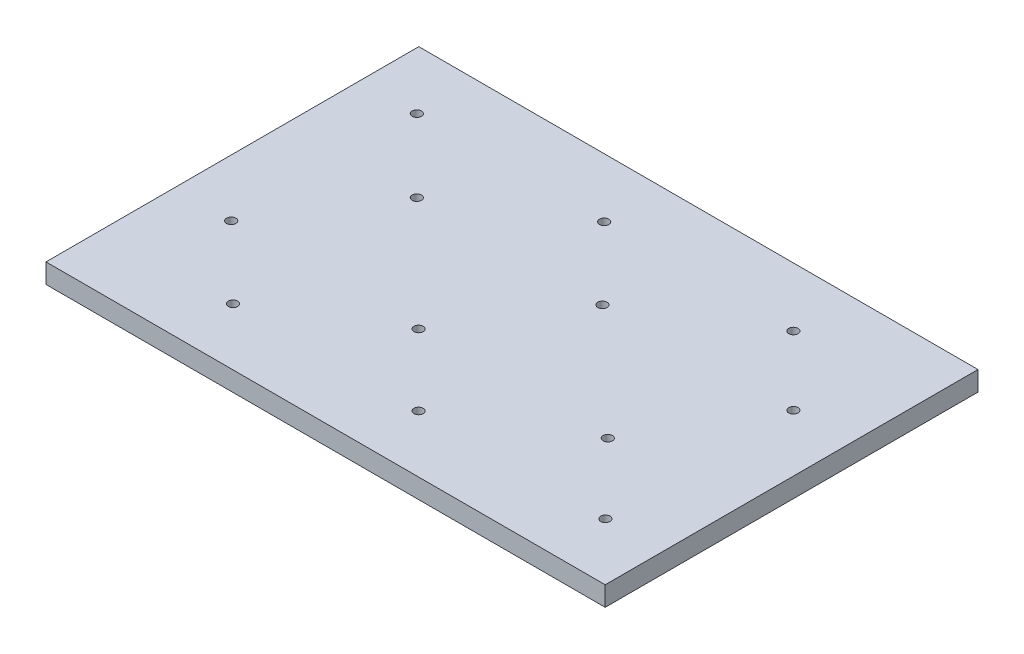
SolidWorks part; units mm, degrees
ref_plane "Front Plane" through (0, 0, 0) normal (0, 0, 1) x (1, 0, 0)
ref_plane "Top Plane" through (0, 0, 0) normal (0, 1, 0) x (1, 0, 0)
ref_plane "Right Plane" through (0, 0, 0) normal (1, 0, 0) x (0, 0, -1)
sketch "Sketch1" plane through (0, 0, 0) normal (0, 1, 0) x (1, 0, 0)
  line L1 (-35, 25) -> (35, 25)
  line L2 (-35, 25) -> (-35, -25)
  line L3 (-35, -25) -> (35, -25)
  line L4 (35, 25) -> (35, -25)
  line L5 (-35, 25) -> (35, -25) construction
  line L6 (-35, -25) -> (35, 25) construction
  point P0 (0, 0)
  dimension "D1" = 70
  dimension "D2" = 50
extrude "Boss-Extrude1" add sketch "Sketch1" along normal blind 6.35
sketch "Sketch2" plane through (0, 6.35, 0) normal (0, 1, 0) x (1, 0, 0)
  line L5 (30, -20) -> (30, 20)
  line L6 (30, -20) -> (30, 20)
  line L11 (30, 20) -> (-30, 20)
  line L12 (-30, 20) -> (-30, -20)
  line L13 (-30, -20) -> (30, -20)
  line L15 (30, 20) -> (-30, 20)
  line L16 (-30, 20) -> (-30, -20)
  line L17 (-30, -20) -> (30, -20)
  dimension "D1" = 5
extrude "Cut-Extrude1" cut sketch "Sketch2" against normal blind 3.175
sketch "Sketch3" plane through (0, 3.175, 0) normal (0, 1, 0) x (1, 0, 0)
  line L1 (-25, 5) -> (-15, 5)
  line L2 (-25, 5) -> (-25, 15)
  line L3 (-25, 15) -> (-15, 15)
  line L4 (-15, 5) -> (-15, 15)
  line L5 (-25, 5) -> (-15, 15) construction
  line L6 (-25, 15) -> (-15, 5) construction
  point P0 (-20, 10)
  dimension "D1" = 10
extrude "Boss-Extrude2" add sketch "Sketch3" along normal blind 0.55
pattern_linear "LPattern1" count 3 spacing 20 along (1, 0, 0) count 2 spacing 20 along (0, 0, 1) of "Boss-Extrude2"
ref_plane "Plane1" through (0, 0, 0) normal (0, 0, 1) x (1, 0, 0)
ref_plane "Plane3" through (0, 0, 0) normal (-1, 0, 0) x (0, 0, 1)
sketch "Sketch10" plane through (0, 3.175, 0) normal (0, 1, 0) x (1, 0, 0)
  line L0 (-10.25, -0.25) -> (-10.25, -20)
  line L1 (-15, 5) -> (-15, 15) construction
  line L2 (-30, 0.25) -> (-10.25, 0.25)
  line L3 (-30, 0.25) -> (-30, -0.25)
  line L4 (-30, -0.25) -> (-10.25, -0.25)
  line L5 (30, 0.25) -> (30, -0.25)
  line L6 (-30, 0.25) -> (30, -0.25) construction
  line L7 (-30, -0.25) -> (30, 0.25) construction
  line L8 (15, 15) -> (15, 5) construction
  line L9 (-10.25, 20) -> (-9.75, 20)
  line L10 (-10.25, 20) -> (-10.25, 0.25)
  line L11 (-10.25, -20) -> (-9.75, -20)
  line L12 (-9.75, 20) -> (-9.75, 0.25)
  line L13 (-10.25, 20) -> (-9.75, -20) construction
  line L14 (-10.25, -20) -> (-9.75, 20) construction
  line L15 (9.8186, 20) -> (10.3186, 20)
  line L16 (9.8186, 20) -> (9.8186, 0.25)
  line L17 (9.6814, -20) -> (10.1814, -20)
  line L18 (10.3186, 20) -> (10.3186, 0.25)
  line L19 (9.8186, 20) -> (10.1814, -20) construction
  line L20 (9.6814, -20) -> (10.3186, 20) construction
  line L22 (-9.75, 0.25) -> (9.8186, 0.25)
  line L24 (-9.75, -0.25) -> (-9.75, -20)
  line L25 (-9.75, -0.25) -> (9.8186, -0.25)
  line L26 (-30, 20) -> (-30, -20) construction
  line L28 (10.3186, 0.25) -> (30, 0.25)
  line L29 (30, 20) -> (-30, 20) construction
  line L30 (10.3186, -0.25) -> (10.1814, -20)
  line L31 (10.3186, -0.25) -> (30, -0.25)
  line L33 (9.8186, -0.25) -> (9.6814, -20)
  point P0 (0, 0)
  point P1 (0, 0)
  point P6 (-10, 0)
  point P11 (10, 0)
  point P13 (-10, 0)
  point P18 (10, 0)
  point P25 (0, 0)
  dimension "D1" = 5
  dimension "D2" = 5
  dimension "D3" = 0.5
extrude "Dividers" add sketch "Sketch10" along normal blind 2 separate body
fillet "Fillet4" radius 3.175 4 edges at (35, 3.175, -25) (-35, 3.175, -25) (-35, 3.175, 25) (35, 3.175, 25)
fillet "Fillet5" [suppressed] radius 1
fillet "Fillet6" radius 3.175 6 edges at (-15, 3.45, -15) (-25, 3.45, -5) (25, 3.45, -15) (15, 3.45, -5) (5, 3.45, -15) (-5, 3.45, -5)
fillet "Fillet7" radius 6.35 6 edges at (25, 3.45, 5) (15, 3.45, 15) (5, 3.45, 5) (-5, 3.45, 15) (-15, 3.45, 5) (-25, 3.45, 15)
sketch "Sketch11" plane through (0, 3.175, 0) normal (0, 1, 0) x (1, 0, 0)
  line L1 (-30.7763, 20.5051) -> (30.7763, 20.5051)
  line L2 (-30.7763, 20.5051) -> (-30.7763, -20.5051)
  line L3 (-30.7763, -20.5051) -> (30.7763, -20.5051)
  line L4 (30.7763, 20.5051) -> (30.7763, -20.5051)
  line L5 (-30.7763, 20.5051) -> (30.7763, -20.5051) construction
  line L6 (-30.7763, -20.5051) -> (30.7763, 20.5051) construction
  point P0 (0, 0)
extrude "Boss-Extrude3" add sketch "Sketch11" along normal blind 2.1 separate body
combine bodies "Combine1" operation type subtract main body 117 bodies to subtract 104
hole_wizard "Ø1.0mm Dowel Hole1" positions "Sketch12" profile "Sketch13" hole size "Ø1.0" standard "ANSI Metric" end condition through all
sketch "Sketch12" plane through (0, 5.275, 0) normal (0, 1, 0) x (1, 0, 0)
  point P0 (-23.8826, 13.6701)
  point P2 (-16.0711, 5.8586)
  point P4 (-23.8826, -6.2428)
  point P6 (-16.0711, -13.8621)
  point P8 (-3.7777, -6.2428)
  point P10 (3.8417, -13.8621)
  point P12 (3.8417, 5.8586)
  point P14 (-3.7777, 13.6701)
  point P16 (16.5193, 13.6701)
  point P18 (23.8826, 6.3068)
  point P20 (16.5193, -6.2428)
  point P22 (23.8826, -13.8621)
sketch "Sketch13" plane through (-23.8826, 5.275, -13.6701) normal (1, 0, 0) x (0, 0, 1)
  line L0 (0, 0) -> (0, 2.1)
  line L1 (0, 2.1) -> (0.5, 2.1)
  line L2 (0.5, 2.1) -> (0.5, 0)
  line L5 (0.5, 0) -> (0, 0)
  line L11 (0, -6.35) -> (0, 107.95) construction
  dimension "Thru Hole Dia." = 1
  dimension "Thru Hole Depth" = 2.1
equation "\"2.5mmm\"=2"
